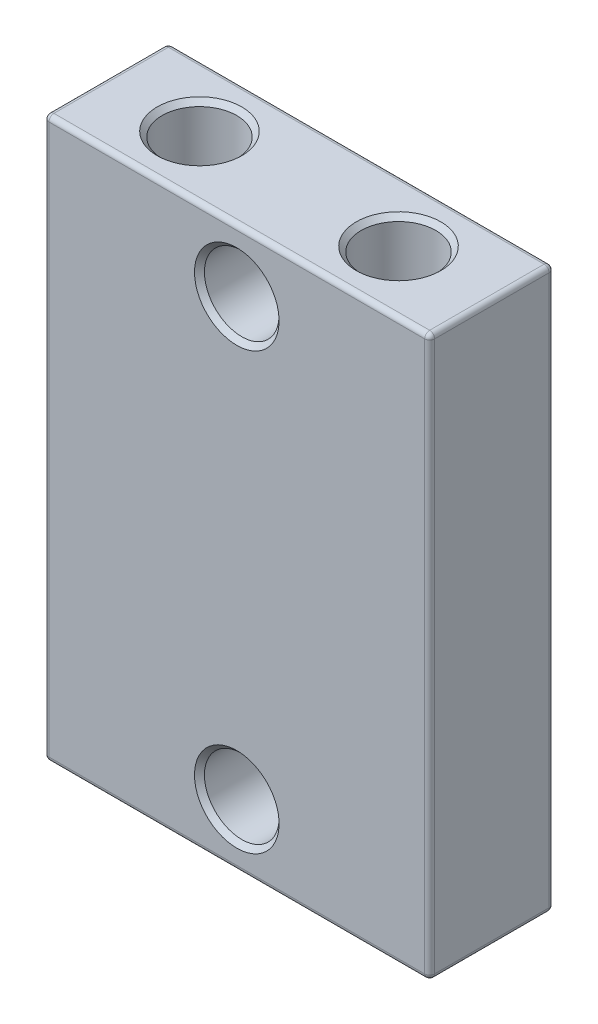
SolidWorks part; units mm, degrees
material "6061 Alloy"
ref_plane "Front Plane" through (0, 0, 0) normal (0, 0, 1) x (1, 0, 0)
ref_plane "Top Plane" through (0, 0, 0) normal (0, 1, 0) x (1, 0, 0)
ref_plane "Right Plane" through (0, 0, 0) normal (1, 0, 0) x (0, 0, -1)
sketch "Sketch1" plane through (0, 0, 0) normal (0, 0, 1) x (1, 0, 0)
  line L1 (-7.75, -11.25) -> (7.75, -11.25)
  line L2 (-7.75, -11.25) -> (-7.75, 11.25)
  line L3 (-7.75, 11.25) -> (7.75, 11.25)
  line L4 (7.75, -11.25) -> (7.75, 11.25)
  line L5 (-7.75, -11.25) -> (7.75, 11.25) construction
  line L6 (-7.75, 11.25) -> (7.75, -11.25) construction
  point P0 (0, 0)
  dimension "D1" = 22.5
  dimension "D2" = 15.5
extrude "Boss-Extrude1" add sketch "Sketch1" along normal blind 5
sketch "Sketch2" plane through (0, 0, 5) normal (0, 0, 1) x (1, 0, 0)
  line L0 (0, 11.25) -> (0, 8.75) construction
  line L1 (7.75, 11.25) -> (-7.75, 11.25) construction
  line L2 (0, -11.25) -> (0, -8.75) construction
  line L3 (-7.75, -11.25) -> (7.75, -11.25) construction
  circle A0 centre (0, 8.75) radius 1.5
  circle A1 centre (0, -8.75) radius 1.5
  dimension "D2" = 3
  dimension "D1" = 2.5
extrude "Cut-Extrude1" cut sketch "Sketch2" against normal through all
sketch "Sketch3" plane through (0, 11.25, 0) normal (0, 1, 0) x (1, 0, 0)
  line L0 (-7.75, -2.5) -> (-4, -2.5) construction
  line L1 (-7.75, -5) -> (-7.75, 0) construction
  line L2 (7.75, -2.5) -> (4, -2.5) construction
  line L3 (7.75, -5) -> (7.75, 0) construction
  circle A0 centre (-4, -2.5) radius 1.5
  circle A1 centre (4, -2.5) radius 1.5
  dimension "D2" = 3
  dimension "D1" = 3.75
extrude "Cut-Extrude2" cut sketch "Sketch3" against normal blind 8
fillet "Fillet1" radius 0.2 12 edges at (7.75, 0, 5) (7.75, 11.25, 2.5) (7.75, 0, 0) (0, -11.25, 5) (7.75, -11.25, 2.5) (0, -11.25, 0) (-7.75, 11.25, 2.5) (-7.75, 0, 5) (-7.75, -11.25, 2.5) (-7.75, 0, 0) (0, 11.25, 5) (0, 11.25, 0)
chamfer "Chamfer1" distance 0.2 angle 45 5 edges at (1.5, -8.75, 5) (4, 11.25, 4) (-4, 11.25, 4) (1.5, 8.75, 5) (1.5, 8.75, 0)
